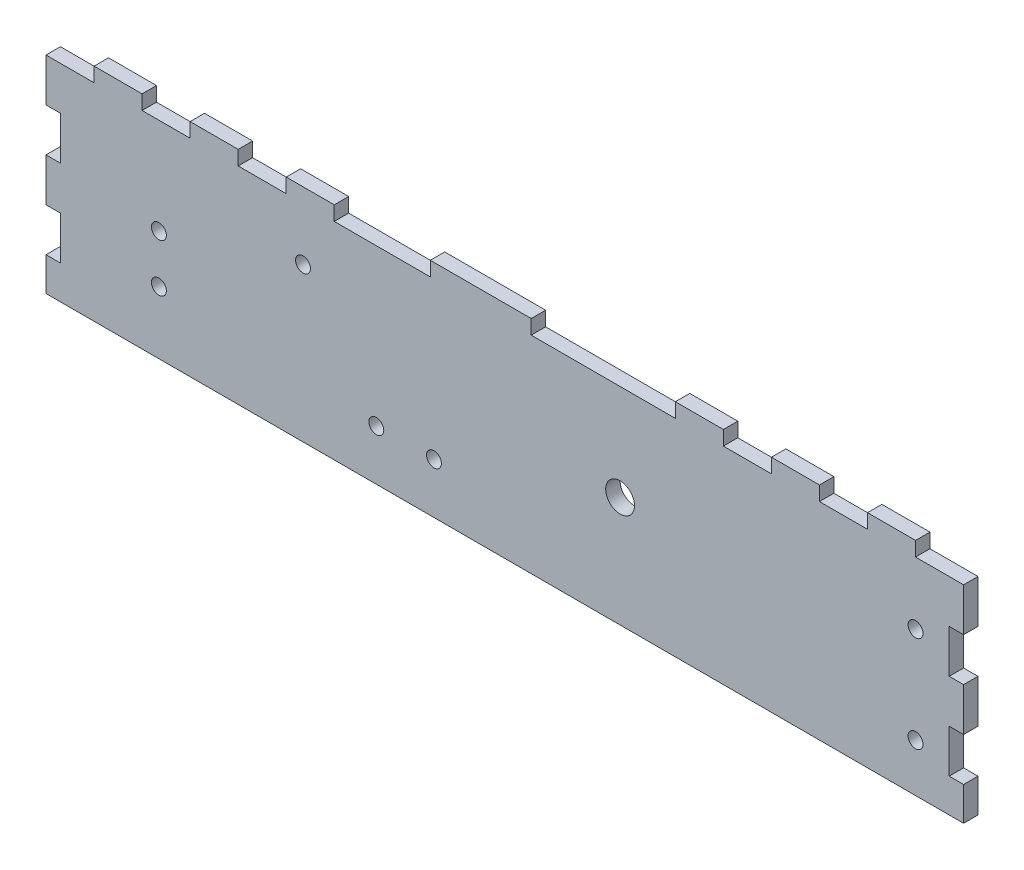
SolidWorks part; units mm, degrees
ref_plane "Front Plane" through (0, 0, 0) normal (0, 0, 1) x (1, 0, 0)
ref_plane "Top Plane" through (0, 0, 0) normal (0, 1, 0) x (1, 0, 0)
ref_plane "Right Plane" through (0, 0, 0) normal (1, 0, 0) x (0, 0, -1)
sketch "Sketch1" plane through (0, 0, 0) normal (0, 0, 1) x (1, 0, 0)
  line L4 (0, 0) -> (191, 0)
  line L5 (191, 0) -> (191, 46)
  line L6 (191, 46) -> (0, 46)
  line L7 (0, 46) -> (0, 0)
  line L8 (0, 0) -> (191, 0)
  line L9 (191, 0) -> (191, 46)
  line L10 (191, 46) -> (0, 46)
  line L11 (0, 46) -> (0, 0)
  circle A0 centre (181, 30) radius 1.55 construction
  circle A1 centre (181, 10) radius 1.55 construction
  circle A2 centre (181, 30) radius 1.55
  circle A3 centre (181, 10) radius 1.55
  dimension "D1" = 0
extrude "Boss-Extrude1" add sketch "Sketch1" along normal blind 3
sketch "Sketch3" plane through (0, 0, 3) normal (0, 0, 1) x (1, 0, 0)
  line L0 (119.5, 46) -> (119.5, 0) construction
  line L1 (119.5, 46) -> (119.5, 0)
  point P2 (119.5, 23)
ref_point "MountPoint-Sus"
sketch "Sketch4" plane through (0, 0, 0) normal (0, 0, -1) x (-1, 0, 0)
  line L0 (-10, 43) -> (-10, 46) construction
  line L1 (-10, 46) -> (0, 46) construction
  line L2 (0, 46) -> (0, 43) construction
  line L3 (0, 43) -> (-10, 43) construction
  line L4 (-30, 43) -> (-30, 46) construction
  line L5 (-30, 46) -> (-20, 46) construction
  line L6 (-20, 46) -> (-20, 43) construction
  line L7 (-20, 43) -> (-30, 43) construction
  line L8 (-50, 43) -> (-50, 46) construction
  line L9 (-50, 46) -> (-40, 46) construction
  line L10 (-40, 46) -> (-40, 43) construction
  line L11 (-40, 43) -> (-50, 43) construction
  line L12 (-60, 43) -> (-80, 43) construction
  line L13 (-80, 43) -> (-80, 46) construction
  line L14 (-80, 46) -> (-60, 46) construction
  line L15 (-60, 46) -> (-60, 43) construction
  line L16 (-131, 43) -> (-131, 46) construction
  line L17 (-131, 46) -> (-101, 46) construction
  line L18 (-101, 46) -> (-101, 43) construction
  line L19 (-101, 43) -> (-131, 43) construction
  line L20 (-151, 43) -> (-151, 46) construction
  line L21 (-151, 46) -> (-141, 46) construction
  line L22 (-141, 46) -> (-141, 43) construction
  line L23 (-141, 43) -> (-151, 43) construction
  line L24 (-171, 43) -> (-171, 46) construction
  line L25 (-171, 46) -> (-161, 46) construction
  line L26 (-161, 46) -> (-161, 43) construction
  line L27 (-161, 43) -> (-171, 43) construction
  line L28 (-191, 46) -> (-181, 46) construction
  line L29 (-181, 46) -> (-181, 43) construction
  line L30 (-181, 43) -> (-191, 43) construction
  line L31 (-191, 43) -> (-191, 46) construction
  line L32 (-10, 43) -> (-10, 46)
  line L33 (-10, 46) -> (0, 46)
  line L34 (0, 46) -> (0, 43)
  line L35 (0, 43) -> (-10, 43)
  line L36 (-30, 43) -> (-30, 46)
  line L37 (-30, 46) -> (-20, 46)
  line L38 (-20, 46) -> (-20, 43)
  line L39 (-20, 43) -> (-30, 43)
  line L40 (-50, 43) -> (-50, 46)
  line L41 (-50, 46) -> (-40, 46)
  line L42 (-40, 46) -> (-40, 43)
  line L43 (-40, 43) -> (-50, 43)
  line L44 (-60, 43) -> (-80, 43)
  line L45 (-80, 43) -> (-80, 46)
  line L46 (-80, 46) -> (-60, 46)
  line L47 (-60, 46) -> (-60, 43)
  line L48 (-131, 43) -> (-131, 46)
  line L49 (-131, 46) -> (-101, 46)
  line L50 (-101, 46) -> (-101, 43)
  line L51 (-101, 43) -> (-131, 43)
  line L52 (-151, 43) -> (-151, 46)
  line L53 (-151, 46) -> (-141, 46)
  line L54 (-141, 46) -> (-141, 43)
  line L55 (-141, 43) -> (-151, 43)
  line L56 (-171, 43) -> (-171, 46)
  line L57 (-171, 46) -> (-161, 46)
  line L58 (-161, 46) -> (-161, 43)
  line L59 (-161, 43) -> (-171, 43)
  line L60 (-191, 46) -> (-181, 46)
  line L61 (-181, 46) -> (-181, 43)
  line L62 (-181, 43) -> (-191, 43)
  line L63 (-191, 43) -> (-191, 46)
extrude "Cut-Extrude1" cut sketch "Sketch4" against normal up to next
sketch "Sketch5" plane through (0, 0, 0) normal (0, 0, -1) x (-1, 0, 0)
  line L4 (0, 34) -> (-3, 34)
  line L5 (0, 25) -> (0, 34)
  line L6 (-3, 25) -> (0, 25)
  line L7 (-3, 34) -> (-3, 25)
  line L8 (0, 34) -> (-3, 34)
  line L9 (0, 25) -> (0, 34)
  line L10 (-3, 25) -> (0, 25)
  line L11 (-3, 34) -> (-3, 25)
  line L12 (-3, 7) -> (0, 7)
  line L13 (0, 7) -> (0, 16)
  line L14 (0, 16) -> (-3, 16)
  line L15 (-3, 16) -> (-3, 7)
  line L16 (-3, 7) -> (0, 7)
  line L17 (0, 7) -> (0, 16)
  line L18 (0, 16) -> (-3, 16)
  line L19 (-3, 16) -> (-3, 7)
  dimension "D1" = 0
  dimension "D2" = 0
extrude "Cut-Extrude2" cut sketch "Sketch5" against normal up to next
sketch "Sketch6" plane through (0, 0, 0) normal (0, 0, -1) x (-1, 0, 0)
  line L0 (-188, 25) -> (-188, 34) construction
  line L1 (-188, 34) -> (-191, 34) construction
  line L2 (-191, 25) -> (-188, 25) construction
  line L3 (-188, 16) -> (-191, 16) construction
  line L4 (-188, 7) -> (-188, 16) construction
  line L5 (-191, 7) -> (-188, 7) construction
  line L6 (-188, 25) -> (-188, 34)
  line L7 (-188, 34) -> (-191, 34)
  line L8 (-191, 25) -> (-188, 25)
  line L9 (-188, 16) -> (-191, 16)
  line L10 (-188, 7) -> (-188, 16)
  line L11 (-191, 7) -> (-188, 7)
  line L40 (-3, 7) -> (-3, 16)
  line L41 (-3, 16) -> (0, 16)
  line L42 (0, 16) -> (0, 25)
  line L43 (0, 25) -> (-3, 25)
  line L44 (-3, 25) -> (-3, 34)
  line L45 (-3, 34) -> (0, 34)
  line L46 (0, 34) -> (0, 43)
  line L47 (0, 43) -> (-10, 43)
  line L48 (-10, 43) -> (-10, 46)
  line L49 (-10, 46) -> (-20, 46)
  line L50 (-20, 46) -> (-20, 43)
  line L51 (-20, 43) -> (-30, 43)
  line L52 (-30, 43) -> (-30, 46)
  line L53 (-30, 46) -> (-40, 46)
  line L54 (-40, 46) -> (-40, 43)
  line L55 (-40, 43) -> (-50, 43)
  line L56 (-50, 43) -> (-50, 46)
  line L57 (-50, 46) -> (-60, 46)
  line L58 (-60, 46) -> (-60, 43)
  line L59 (-60, 43) -> (-80, 43)
  line L60 (-80, 43) -> (-80, 46)
  line L61 (-80, 46) -> (-101, 46)
  line L62 (-101, 46) -> (-101, 43)
  line L63 (-101, 43) -> (-131, 43)
  line L64 (-131, 43) -> (-131, 46)
  line L65 (-131, 46) -> (-141, 46)
  line L66 (-141, 46) -> (-141, 43)
  line L67 (-141, 43) -> (-151, 43)
  line L68 (-151, 43) -> (-151, 46)
  line L69 (-151, 46) -> (-161, 46)
  line L70 (-161, 46) -> (-161, 43)
  line L71 (-161, 43) -> (-171, 43)
  line L72 (-171, 43) -> (-171, 46)
  line L73 (-171, 46) -> (-181, 46)
  line L74 (-181, 46) -> (-181, 43)
  line L75 (-181, 43) -> (-191, 43)
  line L76 (-191, 43) -> (-191, 0)
  line L77 (-191, 0) -> (0, 0)
  line L78 (0, 0) -> (0, 7)
  line L79 (0, 7) -> (-3, 7)
  line L80 (-3, 7) -> (-3, 16)
  line L81 (-3, 16) -> (0, 16)
  line L82 (0, 16) -> (0, 25)
  line L83 (0, 25) -> (-3, 25)
  line L84 (-3, 25) -> (-3, 34)
  line L85 (-3, 34) -> (0, 34)
  line L86 (0, 34) -> (0, 43)
  line L87 (0, 43) -> (-10, 43)
  line L88 (-10, 43) -> (-10, 46)
  line L89 (-10, 46) -> (-20, 46)
  line L90 (-20, 46) -> (-20, 43)
  line L91 (-20, 43) -> (-30, 43)
  line L92 (-30, 43) -> (-30, 46)
  line L93 (-30, 46) -> (-40, 46)
  line L94 (-40, 46) -> (-40, 43)
  line L95 (-40, 43) -> (-50, 43)
  line L96 (-50, 43) -> (-50, 46)
  line L97 (-50, 46) -> (-60, 46)
  line L98 (-60, 46) -> (-60, 43)
  line L99 (-60, 43) -> (-80, 43)
  line L100 (-80, 43) -> (-80, 46)
  line L101 (-80, 46) -> (-101, 46)
  line L102 (-101, 46) -> (-101, 43)
  line L103 (-101, 43) -> (-131, 43)
  line L104 (-131, 43) -> (-131, 46)
  line L105 (-131, 46) -> (-141, 46)
  line L106 (-141, 46) -> (-141, 43)
  line L107 (-141, 43) -> (-151, 43)
  line L108 (-151, 43) -> (-151, 46)
  line L109 (-151, 46) -> (-161, 46)
  line L110 (-161, 46) -> (-161, 43)
  line L111 (-161, 43) -> (-171, 43)
  line L112 (-171, 43) -> (-171, 46)
  line L113 (-171, 46) -> (-181, 46)
  line L114 (-181, 46) -> (-181, 43)
  line L115 (-181, 43) -> (-191, 43)
  line L116 (-191, 43) -> (-191, 0)
  line L117 (-191, 0) -> (0, 0)
  line L118 (0, 0) -> (0, 7)
  line L119 (0, 7) -> (-3, 7)
  line M78 (-191, 43) -> (-191, 0)
  dimension "D1" = 0
extrude "Cut-Extrude3" cut sketch "Sketch6" against normal up to next contours L8 L6 L7 M78 | L11 L10 L9 M78
sketch "Sketch7" plane through (0, 0, 3) normal (0, 0, 1) x (1, 0, 0)
  circle A0 centre (119.5, 23) radius 3
  point P0 (119.5, 23)
  dimension "D1" = 6
extrude "Cut-Extrude4" cut sketch "Sketch7" against normal up to next
sketch "Sketch8" plane through (0, 0, 3) normal (0, 0, 1) x (1, 0, 0)
  circle A0 centre (23.5, 13) radius 1.55 construction
  circle A1 centre (23.5, 23) radius 1.55 construction
  circle A2 centre (53.5, 32) radius 1.55 construction
  circle A3 centre (68.7574, 10.5) radius 1.55 construction
  circle A4 centre (80.7574, 10.5) radius 1.55 construction
  circle A5 centre (23.5, 13) radius 1.55
  circle A6 centre (23.5, 23) radius 1.55
  circle A7 centre (53.5, 32) radius 1.55
  circle A8 centre (68.7574, 10.5) radius 1.55
  circle A9 centre (80.7574, 10.5) radius 1.55
extrude "Cut-Extrude5" cut sketch "Sketch8" against normal up to next
